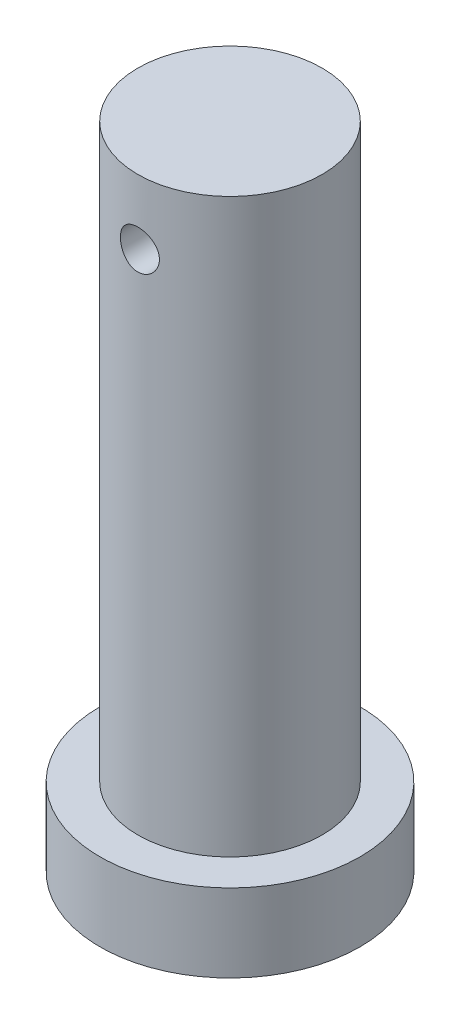
SolidWorks part; units mm, degrees
material "Galvanized Steel"
ref_plane "Front Plane" through (0, 0, 0) normal (0, 0, 1) x (1, 0, 0)
ref_plane "Top Plane" through (0, 0, 0) normal (0, 1, 0) x (1, 0, 0)
ref_plane "Right Plane" through (0, 0, 0) normal (1, 0, 0) x (0, 0, -1)
sketch "Sketch2" plane through (0, 0, 0) normal (0, 0, 1) x (1, 0, 0)
  line L0 (0, 0) -> (25, 0)
  line L1 (25, 0) -> (25, 15)
  line L2 (25, 15) -> (17.7222, 15)
  line L3 (17.7222, 15) -> (17.7222, 125)
  line L4 (17.7222, 125) -> (0, 125)
  line L5 (0, 125) -> (0, 0)
  dimension "D1" = 25
  dimension "D2" = 15
  dimension "D3" = 110
  dimension "D4" = 17.7222
revolve "Revolve1" add sketch "Sketch2" angle 360 about L5
sketch "Sketch3" plane through (0, 0, 0) normal (0, 0, 1) x (1, 0, 0)
  line L0 (17.7222, 125) -> (-17.7222, 125) construction
  line L1 (17.7222, 125) -> (-17.7222, 125) construction
  line L2 (0, 125) -> (0, 112.5) construction
  circle A0 centre (0, 112.5) radius 3.75
  dimension "D2" = 7.5
  dimension "D1" = 12.5
extrude "Cut-Extrude1" cut sketch "Sketch3" against normal through all both and the other way through all
equation "\"D3@Sketch2\"=90+\"D2@Sketch2\"+5"
equation "\"D4@Sketch2\"=35.4444/2"
equation "\"D1@Sketch3\"=5+(15/2)"
